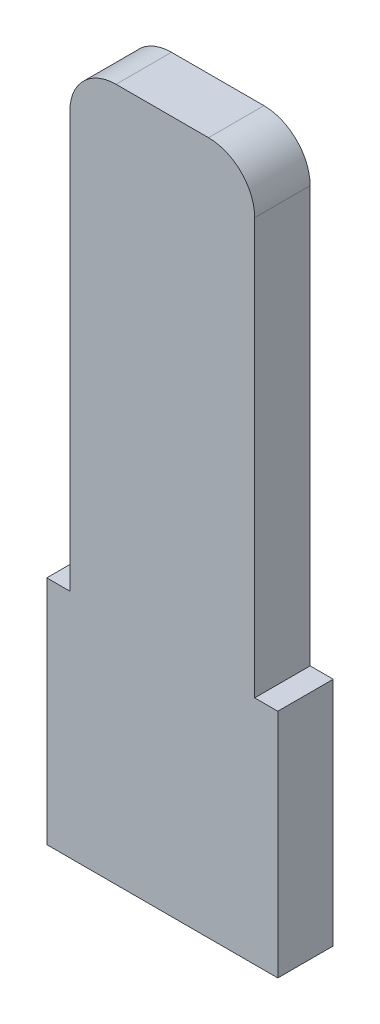
SolidWorks part; units mm, degrees
ref_plane "Ebene vorne" through (0, 0, 0) normal (0, 0, 1) x (1, 0, 0)
ref_plane "Ebene oben" through (0, 0, 0) normal (0, 1, 0) x (1, 0, 0)
ref_plane "Ebene rechts" through (0, 0, 0) normal (1, 0, 0) x (0, 0, -1)
sketch "glider-sketch" plane through (0, 0, 0) normal (0, 0, 1) x (1, 0, 0)
  line L1 (-2.5, 2.5) -> (-2, 2.5)
  line L2 (-2.5, 2.5) -> (-2.5, -2.5)
  line L3 (-2.5, -2.5) -> (2.5, -2.5)
  line L4 (2.5, 2.5) -> (2.5, -2.5)
  line L7 (2, 2.5) -> (2.5, 2.5)
  line L9 (-2, 2.5) -> (-2, 12.5)
  line L10 (-2, 12.5) -> (2, 12.5)
  line L11 (2, 2.5) -> (2, 12.5)
  point P0 (0, 0)
  dimension "D1" = 5
  dimension "D2" = 5
  dimension "D5" = 10
  dimension "D6" = 4
extrude "Aufsatz-Linear austragen1" add sketch "glider-sketch" along normal mid plane 1.2
fillet "Verrundung1" radius 1 1 edges at (2, 12.5, 0)
fillet "Verrundung2" radius 1 1 edges at (-2, 12.5, 0)
